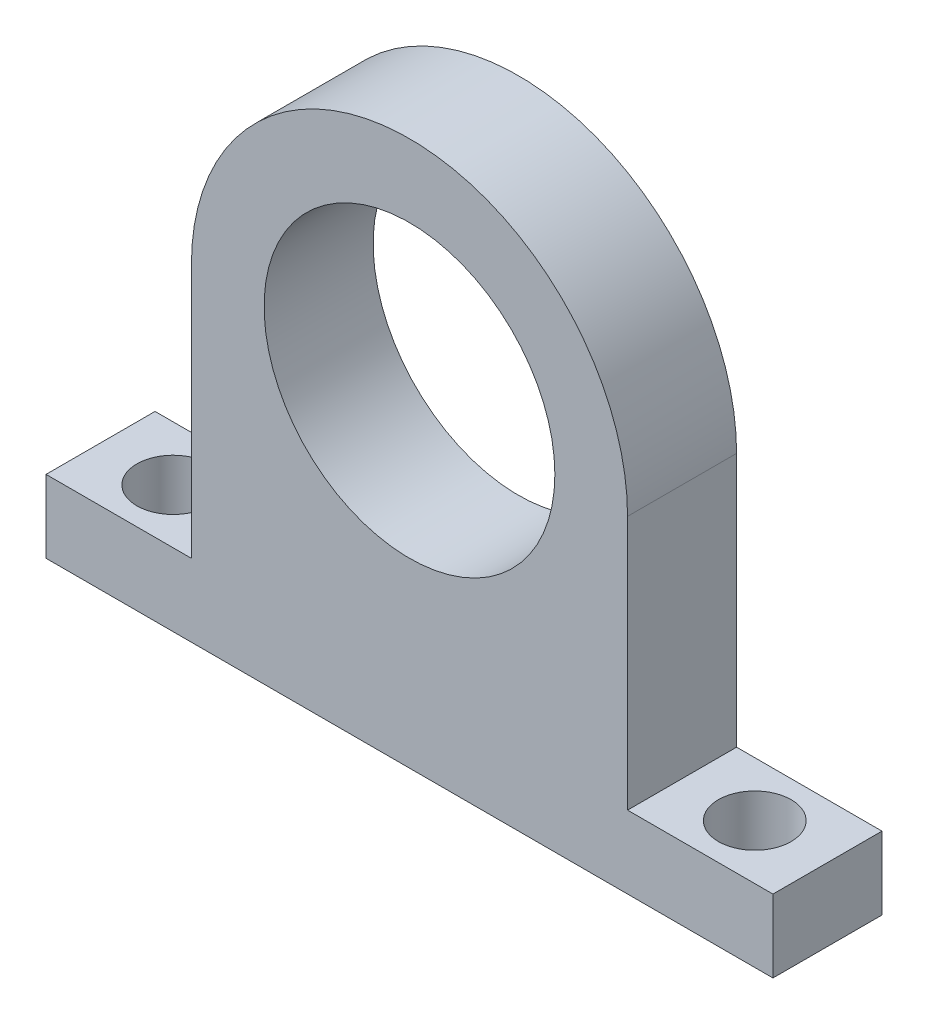
SolidWorks part; units mm, degrees
ref_plane "Front Plane" through (0, 0, 0) normal (0, 0, 1) x (1, 0, 0)
ref_plane "Top Plane" through (0, 0, 0) normal (0, 1, 0) x (1, 0, 0)
ref_plane "Right Plane" through (0, 0, 0) normal (1, 0, 0) x (0, 0, -1)
sketch "Sketch1" plane through (0, 0, 0) normal (0, 0, 1) x (1, 0, 0)
  line L1 (-10, 0) -> (10, 0)
  line L2 (-10, 0) -> (-10, 2)
  line L3 (-10, 2) -> (10, 2)
  line L4 (10, 0) -> (10, 2)
  line L5 (-6, 9) -> (6, 9)
  line L6 (-6, 9) -> (-6, 2)
  line L7 (-6, 2) -> (6, 2)
  line L8 (6, 9) -> (6, 2)
  circle A0 centre (0, 9) radius 6
  circle A1 centre (0, 9) radius 4
  point P12 (0, 0)
  point P13 (0, 2)
  point P14 (0, 0)
  point P15 (0, 0)
  point P16 (0, 0)
  point P17 (0, 0)
  dimension "D1" = 8
  dimension "D2" = 12
  dimension "D3" = 2
  dimension "D4" = 7
  dimension "D5" = 20
extrude "Boss-Extrude1" add sketch "Sketch1" along normal blind 3 contours L1 L4 L3 L2 | A0 L6 L3 L8 | A1 L5 A0 | A1 L5 A0
sketch "Sketch2" plane through (0, 0, 0) normal (0, 1, 0) x (1, 0, 0)
  line L0 (-10, -3) -> (-10, 0) construction
  line L1 (-10, 0) -> (-6, 0) construction
  line L2 (0, -1.65) -> (0, 1.65) construction
  circle A0 centre (-8, -1.5) radius 1
  circle A1 centre (8, -1.5) radius 1
  point P2 (0, 0)
  point P5 (-10, -1.5)
  point P8 (-8, 0)
  dimension "D1" = 2
extrude "Cut-Extrude1" cut sketch "Sketch2" along normal through all
